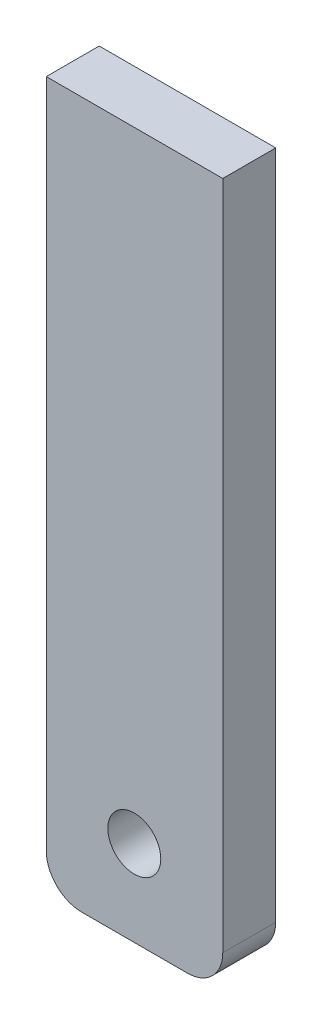
SolidWorks part; units mm, degrees
ref_plane "Front Plane" through (0, 0, 0) normal (0, 0, 1) x (1, 0, 0)
ref_plane "Top Plane" through (0, 0, 0) normal (0, 1, 0) x (1, 0, 0)
ref_plane "Right Plane" through (0, 0, 0) normal (1, 0, 0) x (0, 0, -1)
sketch "Sketch1" plane through (0, 0, 0) normal (0, 0, 1) x (1, 0, 0)
  line L146 (75.2248, 1.7416) -> (65.2248, 1.7416)
  line L147 (65.2248, -36.2584) -> (65.2248, 1.7416)
  line L160 (75.2248, 1.7416) -> (75.2248, -36.2584)
  line L161 (73.2248, -38.2584) -> (67.2248, -38.2584)
  circle A0 centre (70.2119, -33.405) radius 1.5
  arc A1 (67.2248, -38.2584) -> (65.2248, -36.2584) centre (67.2248, -36.2584) cw
  arc A2 (75.2248, -36.2584) -> (73.2248, -38.2584) centre (73.2248, -36.2584) cw
  point P5 (65.2248, -38.2584)
  dimension "D1" = 40
  dimension "D3" = 3
  dimension "D22" = 10
  dimension "D4" = 2
extrude "Boss-Extrude1" add sketch "Sketch1" along normal blind 3
